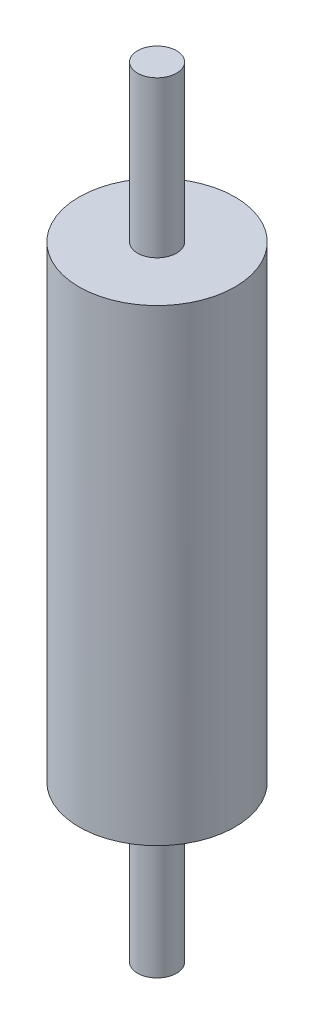
SolidWorks part; units mm, degrees
ref_plane "Front Plane" through (0, 0, 0) normal (0, 0, 1) x (1, 0, 0)
ref_plane "Top Plane" through (0, 0, 0) normal (0, 1, 0) x (1, 0, 0)
ref_plane "Right Plane" through (0, 0, 0) normal (1, 0, 0) x (0, 0, -1)
sketch "Sketch1" plane through (0, 0, 0) normal (0, 1, 0) x (1, 0, 0)
  circle A0 centre (0, 0) radius 10
  dimension "D1" = 20
extrude "Boss-Extrude1" add sketch "Sketch1" along normal blind 100
sketch "Sketch2" plane through (0, 100, 0) normal (0, 1, 0) x (1, 0, 0)
  circle A0 centre (0, 0) radius 2.5
  circle A1 centre (0, 0) radius 10
  dimension "D1" = 5
  dimension "D2" = 20
extrude "Cut-Extrude2" cut sketch "Sketch2" against normal blind 20
sketch "Sketch3" plane through (0, 0, 0) normal (0, -1, 0) x (1, 0, 0)
  circle A0 centre (0, 0) radius 10
  circle A1 centre (0, 0) radius 2.5
  dimension "D1" = 5
  dimension "D2" = 20
extrude "Cut-Extrude3" cut sketch "Sketch3" against normal blind 20
